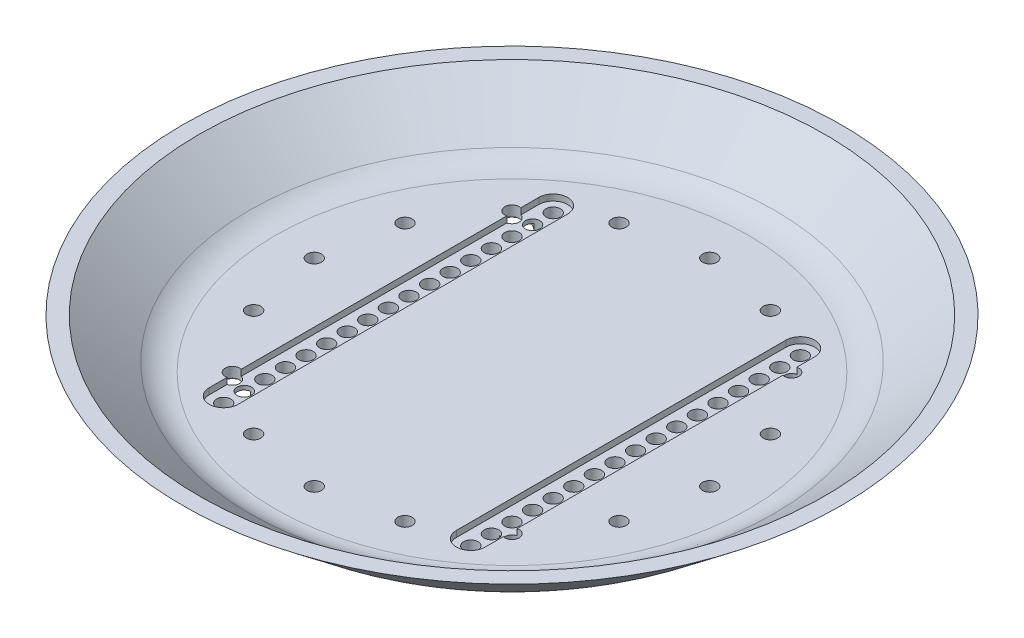
SolidWorks part; units mm, degrees
ref_plane "Front Plane" through (0, 0, 0) normal (0, 0, 1) x (1, 0, 0)
ref_plane "Top Plane" through (0, 0, 0) normal (0, 1, 0) x (1, 0, 0)
ref_plane "Right Plane" through (0, 0, 0) normal (1, 0, 0) x (0, 0, -1)
sketch "Sketch1" plane through (0, 0, 0) normal (0, 0, 1) x (1, 0, 0)
  line L0 (0, 0) -> (-56.4922, 0)
  line L1 (-62.7391, 2.1913) -> (-80, 16)
  line L2 (-80, 16) -> (-75.998, 16)
  line L3 (-75.998, 16) -> (-63.7372, 6.1913)
  line L4 (-57.4902, 4) -> (0, 4)
  line L5 (0, 4) -> (0, 0)
  arc A0 (-56.4922, 0) -> (-62.7391, 2.1913) centre (-56.4922, 10) cw
  arc A1 (-63.7372, 6.1913) -> (-57.4902, 4) centre (-57.4902, 14) ccw
  point P9 (-60, 0)
  dimension "D6" = 10
  dimension "D1" = 4
  dimension "D2" = 2.5
  dimension "D3" = 60
  dimension "D4" = 20
  dimension "D5" = 12
revolve "Revolve1" add sketch "Sketch1" angle 360 about L5
sketch "Sketch2" plane through (0, 0, 0) normal (0, -1, 0) x (1, 0, 0)
  line L0 (-30, 0) -> (30, 0) construction
  circle A0 centre (-30, 0) radius 1.75
  circle A1 centre (30, 0) radius 1.75
  dimension "D2" = 3.5
  dimension "D1" = 60
extrude "Cut-Extrude1" cut sketch "Sketch2" against normal through all
pattern_linear "LPattern1" count 9 spacing 5 along (0, 0, 1) count 5 spacing 10 along (0, 0, -1) of "Cut-Extrude1"
sketch "Sketch3" plane through (0, 0, 0) normal (0, -1, 0) x (1, 0, 0)
  line L0 (0, 48) -> (0, 0) construction
  circle A0 centre (0, 48) radius 1.75
  dimension "D1" = 3.5
  dimension "D2" = 48
extrude "Cut-Extrude2" cut sketch "Sketch3" against normal through all
sketch "Sketch4" plane through (0, 0, 0) normal (0, -1, 0) x (1, 0, 0)
  circle A2 centre (0, 48) radius 3.75
  circle A3 centre (0, 48) radius 3.75
  dimension "D1" = 2
extrude "Cut-Extrude3" cut sketch "Sketch4" against normal blind 1.5
pattern_circular "CirPattern1" count 16 over 360 about axis through (0, 0, 0) along (0, 1, 0) of "Cut-Extrude2", "Cut-Extrude3"
sketch "Sketch5" plane through (0, 4, 0) normal (0, 1, 0) x (1, 0, 0)
  line L0 (-30, 40) -> (-30, -40) construction
  line L1 (-26.5, 40) -> (-26.5, -40)
  line L2 (-33.5, 40) -> (-33.5, -40)
  line L3 (30, 40) -> (30, -40) construction
  line L4 (33.5, 40) -> (33.5, -40)
  line L5 (26.5, 40) -> (26.5, -40)
  arc A0 (-26.5, 40) -> (-33.5, 40) centre (-30, 40) ccw
  arc A1 (-33.5, -40) -> (-26.5, -40) centre (-30, -40) ccw
  arc A2 (33.5, 40) -> (26.5, 40) centre (30, 40) ccw
  arc A3 (26.5, -40) -> (33.5, -40) centre (30, -40) ccw
  point P4 (-30, 0)
  point P9 (30, 0)
  dimension "D1" = 3.5
  dimension "D2" = 3.5
extrude "Cut-Extrude4" cut sketch "Sketch5" against normal blind 1.5
